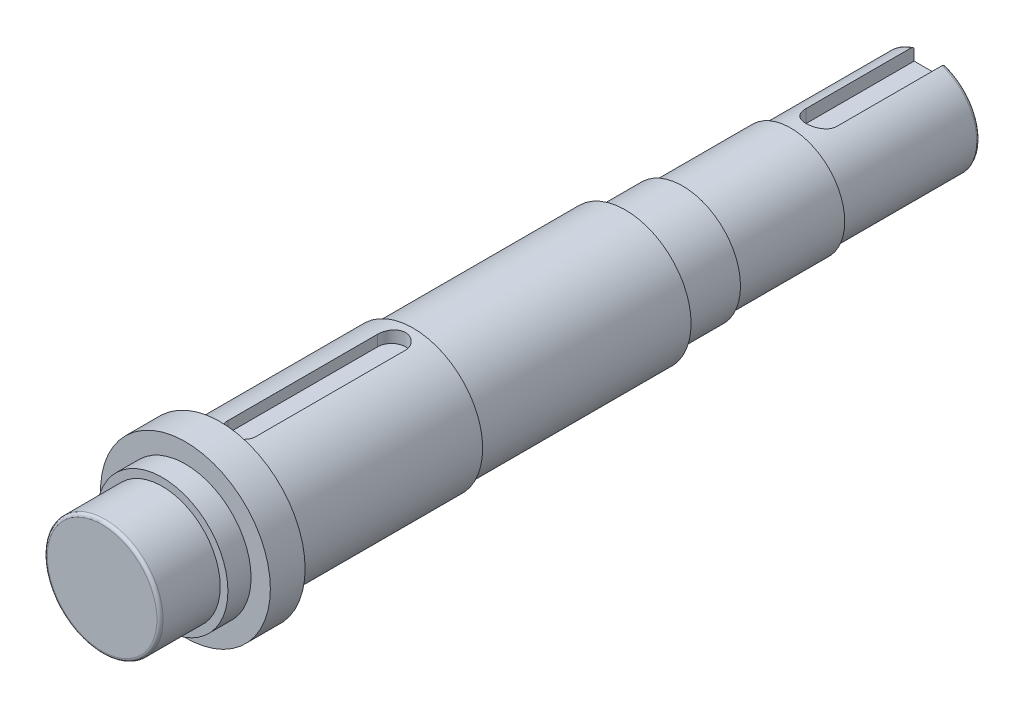
SolidWorks part; units mm, degrees
ref_plane "Front Plane" through (0, 0, 0) normal (0, 0, 1) x (1, 0, 0)
ref_plane "Top Plane" through (0, 0, 0) normal (0, 1, 0) x (1, 0, 0)
ref_plane "Right Plane" through (0, 0, 0) normal (1, 0, 0) x (0, 0, -1)
sketch "Sketch1" plane through (0, 0, 0) normal (1, 0, 0) x (0, 0, -1)
  line L0 (0, 0) -> (536, 0)
  line L1 (536, 0) -> (536, 32.5)
  line L2 (536, 32.5) -> (446, 32.5)
  line L3 (446, 32.5) -> (446, 35)
  line L4 (446, 35) -> (376, 35)
  line L5 (376, 35) -> (376, 37.5)
  line L6 (376, 37.5) -> (339, 37.5)
  line L7 (339, 37.5) -> (339, 42.5)
  line L8 (339, 42.5) -> (201.5, 42.5)
  line L9 (201.5, 42.5) -> (201.5, 45)
  line L10 (201.5, 45) -> (76.5, 45)
  line L11 (76.5, 45) -> (76.5, 55)
  line L12 (76.5, 55) -> (54, 55)
  line L13 (54, 55) -> (54, 42.5)
  line L14 (54, 42.5) -> (39, 42.5)
  line L15 (39, 42.5) -> (39, 37.5)
  line L16 (39, 37.5) -> (0, 37.5)
  line L17 (0, 37.5) -> (0, 0)
  line L18 (0, 0) -> (676.4942, 0) construction
  dimension "D1" = 90
  dimension "D2" = 70
  dimension "D3" = 37
  dimension "D4" = 137.5
  dimension "D5" = 125
  dimension "D6" = 22.5
  dimension "D7" = 15
  dimension "D8" = 39
  dimension "D9" = 65
  dimension "D10" = 70
  dimension "D11" = 75
  dimension "D12" = 85
  dimension "D13" = 90
  dimension "D14" = 110
  dimension "D15" = 85
  dimension "D16" = 75
revolve "Revolve1" add sketch "Sketch1" angle 360 about L18
fillet "Fillet1" radius 2 2 edges at (37.5, 0, 0) (32.5, 0, -536)
sketch "Sketch2" plane through (0, 0, 0) normal (0, 1, 0) x (1, 0, 0)
  line L0 (0, 187.5) -> (0, 90.5) construction
  line L1 (9, 187.5) -> (9, 90.5)
  line L2 (-9, 187.5) -> (-9, 90.5)
  line L3 (45, 201.5) -> (-45, 201.5) construction
  arc A0 (9, 187.5) -> (-9, 187.5) centre (0, 187.5) ccw
  arc A1 (-9, 90.5) -> (9, 90.5) centre (0, 90.5) ccw
  point P3 (0, 139)
  dimension "D1" = 9
  dimension "D2" = 62.5
  dimension "D3" = 97
extrude "Cut-Extrude1" cut sketch "Sketch2" along normal blind 10 from offset 37
sketch "Sketch3" plane through (0, 0, 0) normal (0, 1, 0) x (1, 0, 0)
  line L0 (0, 536) -> (0, 466) construction
  line L1 (30.5, 536) -> (-30.5, 536) construction
  line L2 (10, 536) -> (10, 466)
  line L3 (-10, 536) -> (-10, 466)
  arc A0 (10, 536) -> (-10, 536) centre (0, 536) ccw
  arc A1 (-10, 466) -> (10, 466) centre (0, 466) ccw
  point P5 (0, 501)
  dimension "D1" = 10
  dimension "D2" = 70
extrude "Cut-Extrude2" cut sketch "Sketch3" along normal blind 10 from offset 22.5
equation "\"D3@Sketch2\"=115-18"
